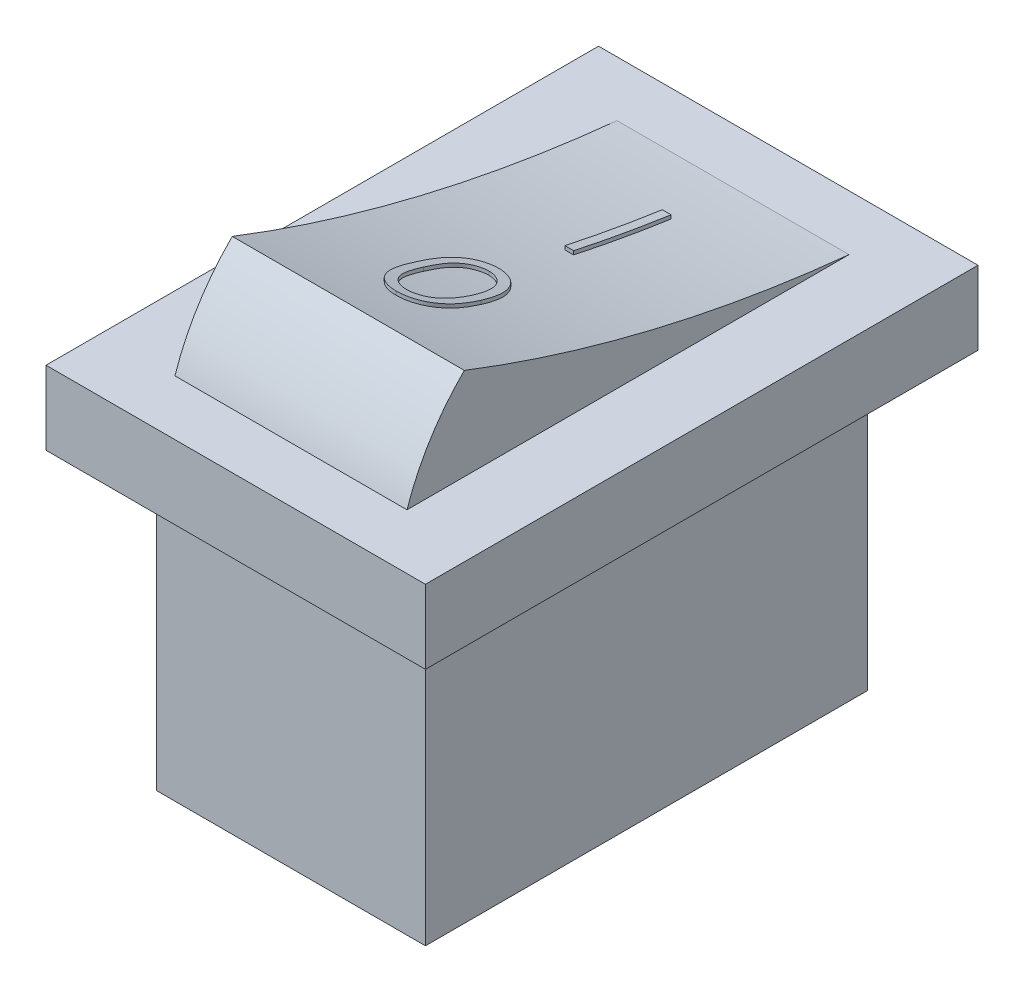
SolidWorks part; units mm, degrees
ref_plane "Front Plane" through (0, 0, 0) normal (0, 0, 1) x (1, 0, 0)
ref_plane "Top Plane" through (0, 0, 0) normal (0, 1, 0) x (1, 0, 0)
ref_plane "Right Plane" through (0, 0, 0) normal (1, 0, 0) x (0, 0, -1)
sketch "Sketch1" plane through (0, 0, 0) normal (0, 1, 0) x (1, 0, 0)
  line L1 (0, 0) -> (10.3, 0)
  line L2 (0, 0) -> (0, 15)
  line L3 (0, 15) -> (10.3, 15)
  line L4 (10.3, 0) -> (10.3, 15)
  dimension "D1" = 10.3
  dimension "D2" = 15
extrude "Boss-Extrude1" add sketch "Sketch1" along normal blind 2
ref_plane "Plane1" through (5.15, 0, 0) normal (1, 0, 0) x (0, 0, -1)
sketch "Sketch2" plane through (5.15, 0, 0) normal (1, 0, 0) x (0, 0, -1)
  line L3 (13.5, 2) -> (1.5, 2)
  line L4 (0, 2) -> (15, 2) construction
  line L5 (15, 2) -> (0, 2) construction
  line L6 (0, 0) -> (15, 0) construction
  arc A0 (3.0559, 4.5) -> (1.5, 2) centre (7.5, 0) ccw
  arc A1 (3.0559, 4.5) -> (13.5, 2) centre (17.4328, 41.4957) ccw
  dimension "D1" = 12
  dimension "D2" = 2.5
extrude "Boss-Extrude2" add sketch "Sketch2" along normal mid plane 6.3
sketch "Sketch3" plane through (0, 0, 0) normal (0, -1, 0) x (1, 0, 0)
  line L4 (0, -15) -> (0, 0) construction
  line L5 (0, 0) -> (10.3, 0) construction
  line L6 (10.3, 0) -> (10.3, -15) construction
  line L12 (1.5, -1.5) -> (1.5, -13.5)
  line L13 (1.5, -13.5) -> (8.8, -13.5)
  line L14 (8.8, -13.5) -> (8.8, -1.5)
  line L15 (8.8, -1.5) -> (1.5, -1.5)
  point P0 (1.5, -7.5)
  point P3 (0, -7.5)
  point P4 (5.15, -1.5)
  point P9 (5.15, 0)
  dimension "D2" = 1.5
  dimension "D1" = 1.5
extrude "Boss-Extrude3" add sketch "Sketch3" along normal blind 8
ref_plane "Plane2" through (0, 2.1, 0) normal (0, 1, 0) x (1, 0, 0)
sketch "Sketch4" plane through (0, 2.1, 0) normal (0, 1, 0) x (1, 0, 0)
  line L0 (0, 9.0544) -> (10.3, 9.0544) construction
  line L1 (0, 15) -> (0, 0) construction
  line L2 (10.3, 0) -> (10.3, 15) construction
  line L3 (0, 4.454) -> (10.3, 4.454) construction
  text T0 "I" font "Century Gothic" height in points 10
  text T1 "0" font "Century Gothic" height in points 10
extrude "Boss-Extrude4" add sketch "Sketch4" along normal offset from surface (0.699 mm away) 0.1
